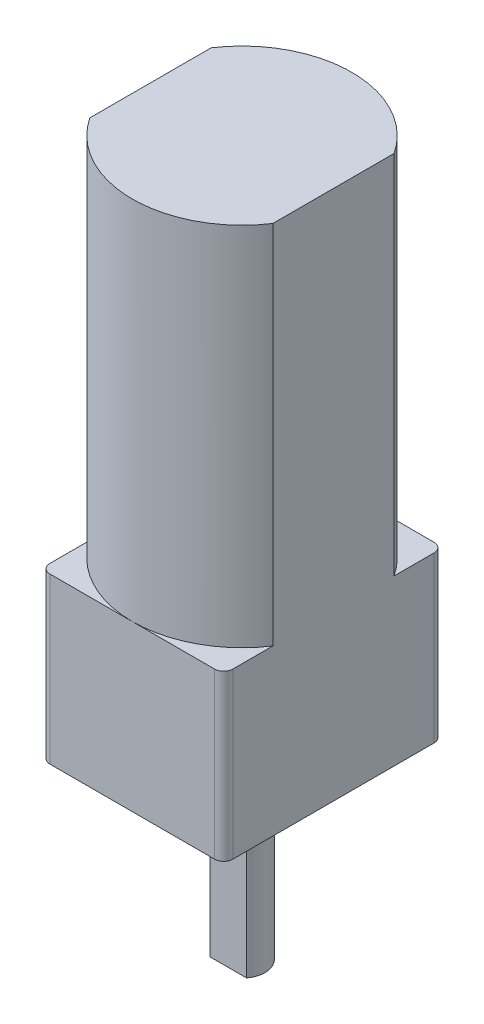
SolidWorks part; units mm, degrees
ref_plane "Front Plane" through (0, 0, 0) normal (0, 0, 1) x (1, 0, 0)
ref_plane "Top Plane" through (0, 0, 0) normal (0, 1, 0) x (1, 0, 0)
ref_plane "Right Plane" through (0, 0, 0) normal (1, 0, 0) x (0, 0, -1)
sketch "Sketch2" plane through (0, 0, 0) normal (0, 1, 0) x (1, 0, 0)
  line L1 (0, 0) -> (-10, 0)
  line L2 (0, 0) -> (0, -12)
  line L3 (0, -12) -> (-10, -12)
  line L4 (-10, 0) -> (-10, -12)
  line L5 (0, 0) -> (-10, -12) construction
  line L6 (0, -12) -> (-10, 0) construction
  point P4 (-5, -6)
  dimension "D1" = 10
  dimension "D2" = 12
extrude "Boss-Extrude1" add sketch "Sketch2" along normal blind 15
fillet "Fillet2" radius 2.5 1 edges at (0, 7.5, 0)
fillet "Fillet3" radius 2.5 1 edges at (-10, 7.5, 0)
fillet "Fillet4" radius 2.5 1 edges at (-10, 7.5, 12)
fillet "Fillet5" radius 2.5 1 edges at (0, 7.5, 12)
sketch "Sketch3" plane through (0, 0, 0) normal (0, -1, 0) x (1, 0, 0)
  line L0 (0, 2.5) -> (-10, 9.5)
  line L1 (-10, 2.5) -> (0, 9.5)
  line L3 (0, 0) -> (-10, 0)
  line L4 (0, 0) -> (0, 12)
  line L5 (0, 12) -> (-10, 12)
  line L6 (-10, 0) -> (-10, 12)
  line L7 (0, 0) -> (-10, 12) construction
  line L8 (0, 12) -> (-10, 0) construction
  point P8 (-5, 6)
  line M3 (0, 2.5) -> (0, 9.5)
  arc M4 (0, 9.5) -> (-2.5, 12) centre (-2.5, 9.5) ccw
  line M5 (-2.5, 12) -> (-7.5, 12)
  arc M6 (-7.5, 12) -> (-10, 9.5) centre (-7.5, 9.5) ccw
  line M7 (-10, 9.5) -> (-10, 2.5)
  arc M8 (-10, 2.5) -> (-7.5, 0) centre (-7.5, 2.5) ccw
  line M9 (-7.5, 0) -> (-2.5, 0)
  arc M10 (-2.5, 0) -> (0, 2.5) centre (-2.5, 2.5) ccw
  dimension "D1" = 10
  dimension "D2" = 12
extrude "Boss-Extrude2" add sketch "Sketch3" along normal blind 9 contours L3 L4 M10 | L1 L0 M8 M9 M10 | L6 L3 M8 | L1 L0 M3 | L1 L0 M7 | L0 L1 M4 M5 M6 | L6 L5 M6 | L4 L5 M4
fillet "Fillet6" radius 0.5 4 edges at (-10, -4.5, 12) (-10, -4.5, 0) (0, -4.5, 12) (0, -4.5, 0)
sketch "Sketch4" plane through (0, -9, 0) normal (0, -1, 0) x (1, 0, 0)
  line L0 (-9.8536, 11.8536) -> (-0.1464, 0.1464)
  line L1 (-0.1464, 11.8536) -> (-9.8536, 0.1464)
  arc A0 (-9.5, 12) -> (-10, 11.5) centre (-9.5, 11.5) ccw construction
  arc A1 (-0.5, 0) -> (0, 0.5) centre (-0.5, 0.5) ccw construction
  arc A2 (0, 11.5) -> (-0.5, 12) centre (-0.5, 11.5) ccw construction
  arc A3 (-10, 0.5) -> (-9.5, 0) centre (-9.5, 0.5) ccw construction
  circle A4 centre (-5, 6) radius 1.25
  circle A5 centre (-5, 6) radius 2
  dimension "D1" = 2.5
  dimension "D2" = 4
extrude "Boss-Extrude4" add sketch "Sketch4" along normal blind 0.8 contours A5 | A4
sketch "Sketch5" plane through (0, -9, 0) normal (0, -1, 0) x (1, 0, 0)
  circle A0 centre (-5, 6) radius 1.25
  circle A1 centre (-5, 6) radius 1.25 construction
  dimension "D2" = 2.5
  dimension "D1" = 0
extrude "Boss-Extrude5" add sketch "Sketch5" along normal blind 10
sketch "Sketch6" plane through (0, -19, 0) normal (0, -1, 0) x (1, 0, 0)
  line L0 (-5, 6) -> (-5, 6.75)
  line L1 (-5, 6.75) -> (-6, 6.75)
  line L2 (-6, 6.75) -> (-4, 6.75)
  circle A0 centre (-5, 6) radius 0.75
  circle A1 centre (-5, 6) radius 1.25 construction
  circle M2 centre (-5, 6) radius 1.25
  dimension "D1" = 0.75
extrude "Cut-Extrude1" cut sketch "Sketch6" against normal blind 9.2 contours L1 L2 M2
sketch "Sketch8" plane through (0, 15, 0) normal (0, 1, 0) x (1, 0, 0)
  line L8 (-7.5, -12) -> (-2.5, -12)
  line L9 (0, -9.5) -> (0, -2.5)
  line L10 (-2.5, 0) -> (-7.5, 0)
  line L11 (-10, -2.5) -> (-10, -9.5)
  line L12 (-7.5, -12) -> (-2.5, -12)
  line L13 (0, -9.5) -> (0, -2.5)
  line L14 (-2.5, 0) -> (-7.5, 0)
  line L15 (-10, -2.5) -> (-10, -9.5)
  arc A8 (-2.5, -12) -> (0, -9.5) centre (-2.5, -9.5) ccw
  arc A9 (0, -2.5) -> (-2.5, 0) centre (-2.5, -2.5) ccw
  arc A10 (-7.5, 0) -> (-10, -2.5) centre (-7.5, -2.5) ccw
  arc A11 (-10, -9.5) -> (-7.5, -12) centre (-7.5, -9.5) ccw
  arc A12 (-2.5, -12) -> (0, -9.5) centre (-2.5, -9.5) ccw
  arc A13 (0, -2.5) -> (-2.5, 0) centre (-2.5, -2.5) ccw
  arc A14 (-7.5, 0) -> (-10, -2.5) centre (-7.5, -2.5) ccw
  arc A15 (-10, -9.5) -> (-7.5, -12) centre (-7.5, -9.5) ccw
  dimension "D1" = 0
extrude "Cut-Extrude2" cut sketch "Sketch8" against normal blind 15
sketch "Sketch9" plane through (0, 0, 0) normal (0, 1, 0) x (1, 0, 0)
  line L0 (-10, -6) -> (-10, -9.5)
  line L1 (-10, -9.5) -> (-10, -2.5)
  line L2 (-10, -6) -> (0, -6)
  line L3 (0, -6) -> (-5, -6)
  line L4 (-9.5, -12) -> (-0.5, -12)
  line L5 (0, -11.5) -> (0, -0.5)
  line L6 (-0.5, 0) -> (-9.5, 0)
  line L7 (-10, -0.5) -> (-10, -11.5)
  line L8 (-9.5, -12) -> (-0.5, -12)
  line L9 (0, -11.5) -> (0, -0.5)
  line L10 (-0.5, 0) -> (-9.5, 0)
  line L11 (-10, -0.5) -> (-10, -11.5)
  arc A0 (-5, -12) -> (0, -9.3166) centre (-5, -6) ccw
  arc A1 (-5, -12) -> (-10, -9.3166) centre (-5, -6) cw
  arc A2 (-5, 0) -> (-10, -2.6834) centre (-5, -6) ccw
  arc A3 (-5, 0) -> (0, -2.6834) centre (-5, -6) cw
  arc A4 (-0.5, -12) -> (0, -11.5) centre (-0.5, -11.5) ccw
  arc A5 (0, -0.5) -> (-0.5, 0) centre (-0.5, -0.5) ccw
  arc A6 (-9.5, 0) -> (-10, -0.5) centre (-9.5, -0.5) ccw
  arc A7 (-10, -11.5) -> (-9.5, -12) centre (-9.5, -11.5) ccw
  arc A8 (-0.5, -12) -> (0, -11.5) centre (-0.5, -11.5) ccw
  arc A9 (0, -0.5) -> (-0.5, 0) centre (-0.5, -0.5) ccw
  arc A10 (-9.5, 0) -> (-10, -0.5) centre (-9.5, -0.5) ccw
  arc A11 (-10, -11.5) -> (-9.5, -12) centre (-9.5, -11.5) ccw
  dimension "D2" = 11
  dimension "D3" = 3.5
  dimension "D4" = 7
  dimension "D1" = 0
extrude "Boss-Extrude7" add sketch "Sketch9" along normal blind 20 contours A1 A0 L9 L2 | A3 A2 L11 L2 L4
